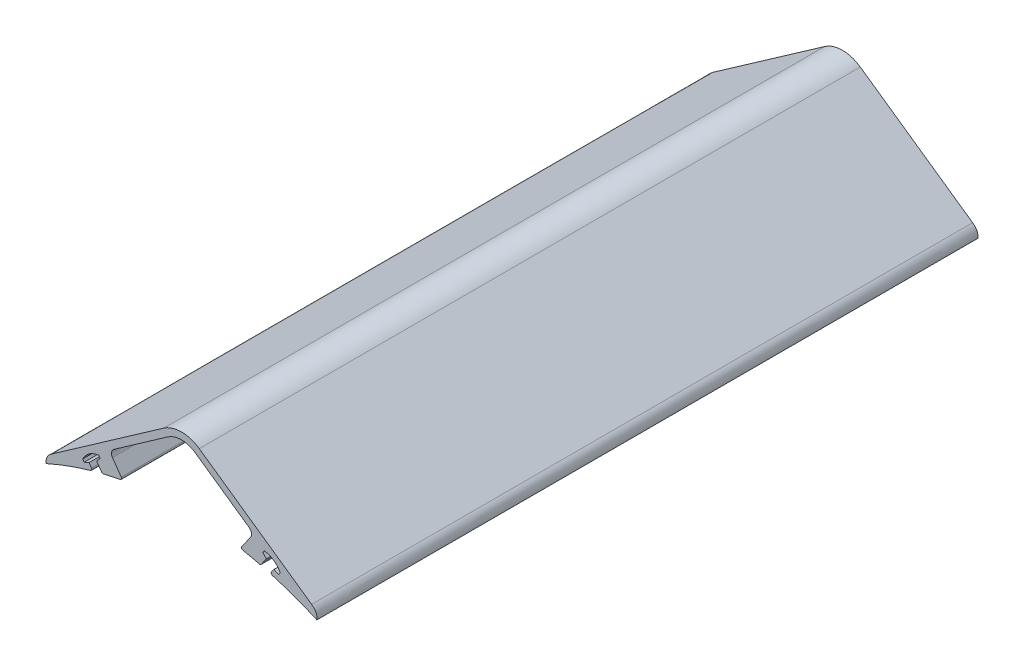
SolidWorks part; units mm, degrees
ref_plane "Front Plane" through (0, 0, 0) normal (0, 0, 1) x (1, 0, 0)
ref_plane "Top Plane" through (0, 0, 0) normal (0, 1, 0) x (1, 0, 0)
ref_plane "Right Plane" through (0, 0, 0) normal (1, 0, 0) x (0, 0, -1)
sketch "Sketch1" plane through (0, 0, 0) normal (0, 0, 1) x (1, 0, 0)
  line L0 (0, 0) -> (0, 152.4) construction
  line L1 (-59.9912, 144.0357) -> (-8.1938, 180.2969)
  line L3 (-6.373, 177.696) -> (-33.3007, 158.8449)
  line L4 (6.373, 177.696) -> (33.3007, 158.8449)
  line L5 (-33.3007, 158.8449) -> (-27.0899, 149.973)
  line L6 (33.3007, 158.8449) -> (27.0899, 149.973)
  line L7 (-36.4912, 147.9667) -> (-39.1424, 151.7538)
  line L8 (-46.5547, 158.6235) -> (-28.8566, 133.3425) construction
  line L9 (-39.1424, 151.7538) -> (-37.4676, 153.5263)
  line L10 (-34.2947, 155.7476) -> (-23.7131, 163.1553) construction
  line L13 (-40.8893, 146.8122) -> (-42.6364, 149.3078)
  line L14 (-42.6364, 149.3078) -> (-44.875, 148.3407)
  line L17 (-37.4676, 153.5263) -> (-38.145, 154.4939)
  line L18 (-44.875, 148.3407) -> (-45.5523, 149.3083)
  line L19 (36.4912, 147.9667) -> (39.1424, 151.7538)
  line L20 (40.8893, 146.8122) -> (42.6364, 149.3078)
  line L21 (44.875, 148.3407) -> (45.5523, 149.3083)
  line L22 (42.6364, 149.3078) -> (44.875, 148.3407)
  line L23 (39.1424, 151.7538) -> (37.4676, 153.5263)
  line L24 (37.4676, 153.5263) -> (38.145, 154.4939)
  line L27 (59.9912, 144.0357) -> (8.1938, 180.2969)
  arc A1 (6.373, 177.696) -> (-6.373, 177.696) centre (0, 168.5925) ccw
  arc A2 (8.1938, 180.2969) -> (-8.1938, 180.2969) centre (0, 168.5925) ccw
  circle A4 centre (0, 168.5925) radius 11.1125 construction
  arc A8 (62.4412, 139.0211) -> (40.8893, 146.8122) centre (0, 0) ccw
  arc A9 (36.4912, 147.9667) -> (27.0899, 149.973) centre (0, 0) ccw
  arc A10 (-40.8893, 146.8122) -> (-62.4412, 139.0211) centre (0, 0) ccw
  arc A11 (-27.0899, 149.973) -> (-36.4912, 147.9667) centre (0, 0) ccw
  circle A12 centre (0, 0) radius 152.4 construction
  spline S0 degree 2 poles (-45.5523, 149.3083) (-43.1806, 153.8037) (-38.145, 154.4939) knots 0 0 0 1 1 1
  spline S1 degree 2 poles (45.5523, 149.3083) (43.1806, 153.8037) (38.145, 154.4939) knots 0 0 0 1 1 1
  spline S2 degree 2 poles (-59.9912, 144.0357) (-62.7825, 142.084) (-62.4412, 139.0211) knots 0 0 0 1 1 1
  spline S3 degree 2 poles (59.9912, 144.0357) (62.7825, 142.084) (62.4412, 139.0211) knots 0 0 0 1 1 1
  dimension "D3" = 22.225
  dimension "D4" = 28.575
  dimension "D17" = 304.8
  dimension "D2" = 168.5925
  dimension "D5" = 10.8299
  dimension "D8" = 43.8553
  dimension "D9" = 9.1452
  dimension "D10" = 3.0464
  dimension "D11" = 4.6229
  dimension "D12" = 2.4386
  dimension "D13" = 1.1811
  dimension "D14" = 2.3424
  dimension "D7" = 24.2562
  dimension "D15" = 1.791
  dimension "D16" = 3.2237
  dimension "D18" = 147.2577
extrude "Boss-Extrude1" add sketch "Sketch1" along normal blind 304.8 contours L1 A2 L27 S3 A8 L20 L22 L21 S1 L24 L23 L19 A9 L6 L4 A1 L3 L5 A11 L7 L9 L17 S0 L18 L14 L13 A10 S2
fillet "Fillet2" radius 2.54 2 edges at (-33.3007, 158.8449, 152.4) (33.3007, 158.8449, 152.4)
fillet "Fillet7" radius 0.762 6 edges at (40.8893, 146.8122, 152.4) (36.4912, 147.9667, 152.4) (27.0899, 149.973, 152.4) (-27.0899, 149.973, 152.4) (-36.4912, 147.9667, 152.4) (-40.8893, 146.8122, 152.4)
equation "\"diameter\"= 12in'diameter of rocket"
equation "\"D2@Sketch1\"= \"diameter\" / 2 + 7 / 16in + .2 'distance of midpoint of pipe to rocket center"
